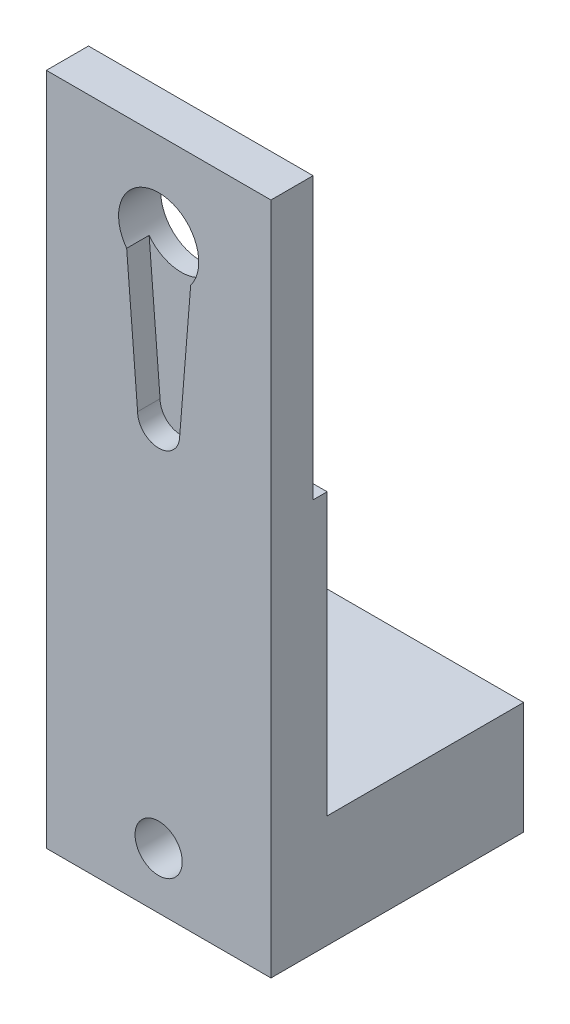
SolidWorks part; units mm, degrees
ref_plane "Front Plane" through (0, 0, 0) normal (0, 0, 1) x (1, 0, 0)
ref_plane "Top Plane" through (0, 0, 0) normal (0, 1, 0) x (1, 0, 0)
ref_plane "Right Plane" through (0, 0, 0) normal (1, 0, 0) x (0, 0, -1)
sketch "Sketch3" plane through (0, 0, 0) normal (0, 0, 1) x (1, 0, 0)
  line L1 (-10, 30) -> (10, 30)
  line L2 (-10, 30) -> (-10, -30)
  line L3 (-10, -30) -> (10, -30)
  line L4 (10, 30) -> (10, -30)
  line L5 (-10, 30) -> (10, -30) construction
  line L6 (-10, -30) -> (10, 30) construction
  point P0 (0, 0)
  dimension "D1" = 20
  dimension "D2" = 60
extrude "Boss-Extrude3" add sketch "Sketch3" along normal blind 5
sketch "Sketch4" plane through (0, 0, 5) normal (0, 0, 1) x (1, 0, 0)
  line L0 (-1.875, 7.7392) -> (1.875, 7.7392)
  line L1 (-2.85, 19.85) -> (2.85, 19.85)
  line L2 (-2.85, 19.85) -> (-1.875, 7.7392)
  line L3 (2.85, 19.85) -> (1.875, 7.7392)
  line L4 (10, -30) -> (10, 30) construction
  line L7 (10, 30) -> (-10, 30) construction
  circle A0 centre (0, 22) radius 3.57
  arc A1 (-1.875, 7.7392) -> (1.875, 7.7392) centre (0, 7.7392) ccw
  dimension "D1" = 7.14
  dimension "D2" = 3.75
  dimension "D3" = 5.7
  dimension "D4" = 12.15
  dimension "D5" = 12.15
  dimension "D6" = 10
  dimension "D7" = 8
extrude "Cut-Extrude2" cut sketch "Sketch4" against normal blind 2 contours L0 A1 | A0 L2 L0 L3
sketch "Sketch6" plane through (0, 0, 3) normal (0, 0, 1) x (1, 0, 0)
  line L0 (10, 30) -> (-10, 30) construction
  line L1 (-10, 30) -> (-10, -30) construction
  circle A0 centre (0, 22) radius 3.57
  dimension "D1" = 7.14
  dimension "D2" = 8
  dimension "D3" = 10
extrude "Cut-Extrude3" cut sketch "Sketch6" against normal blind 3
sketch "Sketch7" plane through (0, 0, 0) normal (0, 0, -1) x (-1, 0, 0)
  line L0 (-10, -30) -> (-10, 30) construction
  line L1 (10, -30) -> (-10, -30)
  line L2 (10, -30) -> (10, -20)
  line L3 (10, -20) -> (-10, -20)
  line L4 (-10, -30) -> (-10, -20)
  dimension "D1" = 10
extrude "Boss-Extrude4" add sketch "Sketch7" along normal blind 17.5
sketch "Sketch8" plane through (0, 0, -17.5) normal (0, 0, -1) x (-1, 0, 0)
  line L1 (10, -30) -> (10, -20) construction
  line L2 (10, -20) -> (-10, -20) construction
  circle A0 centre (0, -25) radius 2.1
  dimension "D1" = 4.2
  dimension "D2" = 10
  dimension "D3" = 5
extrude "Cut-Extrude4" cut sketch "Sketch8" against normal blind 40
sketch "Sketch9" plane through (10, 0, 0) normal (1, 0, 0) x (0, 0, -1)
  line L1 (0, 30) -> (-1.25, 30)
  line L2 (0, 30) -> (0, 5)
  line L3 (0, 5) -> (-1.25, 5)
  line L4 (-1.25, 30) -> (-1.25, 5)
  dimension "D1" = 25
  dimension "D2" = 1.25
extrude "Cut-Extrude5" cut sketch "Sketch9" against normal blind 30
